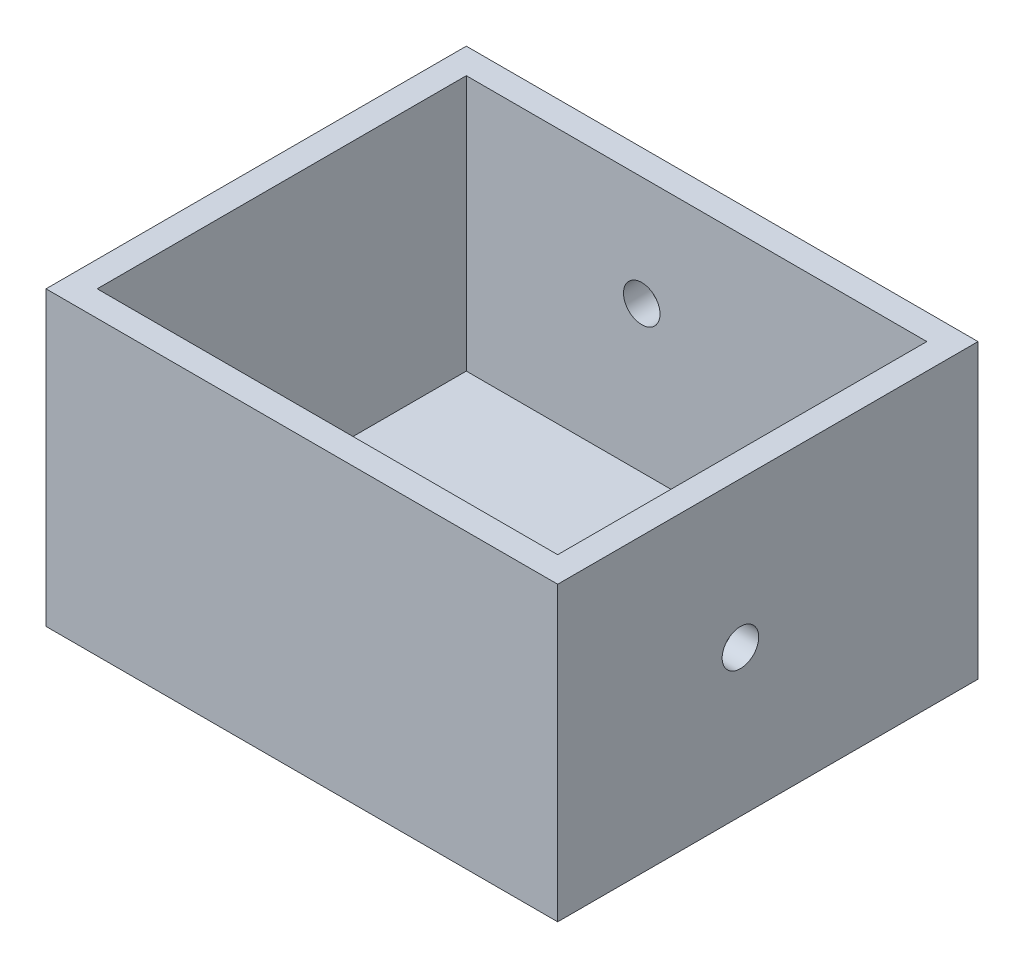
SolidWorks part; units mm, degrees
material "1060 Alloy"
ref_plane "Front Plane" through (0, 0, 0) normal (0, 0, 1) x (1, 0, 0)
ref_plane "Top Plane" through (0, 0, 0) normal (0, 1, 0) x (1, 0, 0)
ref_plane "Right Plane" through (0, 0, 0) normal (1, 0, 0) x (0, 0, -1)
sketch "Sketch1" plane through (0, 0, 0) normal (0, 1, 0) x (1, 0, 0)
  line L1 (-72.7163, -61.4091) -> (67.2837, -61.4091)
  line L2 (-72.7163, -61.4091) -> (-72.7163, 53.5909)
  line L3 (-72.7163, 53.5909) -> (67.2837, 53.5909)
  line L4 (67.2837, -61.4091) -> (67.2837, 53.5909)
  dimension "D1" = 140
  dimension "D2" = 115
extrude "Boss-Extrude1" add sketch "Sketch1" along normal blind 80
ref_plane "Plane1" through (0, 80, 0) normal (0, 1, 0) x (1, 0, 0)
sketch "Sketch2" plane through (0, 80, 0) normal (0, 1, 0) x (1, 0, 0)
  line L0 (67.2837, -61.4091) -> (67.2837, 53.5909) construction
  line L1 (-65.7163, -54.4091) -> (60.2837, -54.4091)
  line L2 (-65.7163, -54.4091) -> (-65.7163, 46.5909)
  line L3 (-65.7163, 46.5909) -> (60.2837, 46.5909)
  line L4 (60.2837, -54.4091) -> (60.2837, 46.5909)
  line L5 (67.2837, 53.5909) -> (-72.7163, 53.5909) construction
  line L6 (-72.7163, 53.5909) -> (-72.7163, -61.4091) construction
  line L7 (-72.7163, -61.4091) -> (67.2837, -61.4091) construction
  dimension "D1" = 7
  dimension "D2" = 7
  dimension "D3" = 7
  dimension "D4" = 7
extrude "Cut-Extrude1" cut sketch "Sketch2" against normal blind 70
ref_plane "Plane2" through (0, 0, -53.5909) normal (0, 0, -1) x (-1, 0, 0)
sketch "Sketch3" plane through (0, 0, -53.5909) normal (0, 0, -1) x (-1, 0, 0)
  line L1 (-67.2837, 80) -> (72.7163, 80) construction
  line L2 (-67.2837, 80) -> (-67.2837, 0) construction
  point P0 (17.7163, 50)
  point P1 (-42.2837, 50)
  dimension "D2" = 60
  dimension "D3" = 30
  dimension "D4" = 25
hole_wizard "M10x1.0 Tapped Hole1" positions "3DSketch1" profile "Sketch4" tap size "M10x1.0" standard "ANSI Metric"
sketch3d "3DSketch1"
  point P0 (-17.7163, 50, -53.5909)
  point P3 (42.2837, 50, -53.5909)
sketch "Sketch4" plane through (-17.7163, 50, -53.5909) normal (1, 0, 0) x (0, 1, 0)
  line L0 (0, 0) -> (0, 25.7039)
  line L1 (0, 25.7039) -> (4.5, 23)
  line L2 (4.5, 23) -> (4.5, 20)
  line L3 (4.5, 20) -> (5, 20)
  line L4 (5, 20) -> (5, 0)
  line L5 (5, 0) -> (0, 0)
  line L10 (0, 25.7039) -> (-4.5, 23) construction
  line L11 (0, -6.35) -> (0, 107.95) construction
  dimension "Tap Drill Dia." = 9
  dimension "Tap Drill Depth" = 23
  dimension "Thread Major Dia." = 10
  dimension "Thread Depth" = 20
  dimension "Drill Angle" = 118
ref_plane "Plane3" through (67.2837, 0, 0) normal (1, 0, 0) x (0, 0, -1)
sketch "Sketch5" plane through (67.2837, 0, 0) normal (1, 0, 0) x (0, 0, -1)
  line L0 (53.5909, 80) -> (53.5909, 0) construction
  line L1 (-61.4091, 80) -> (53.5909, 80) construction
  point P0 (-11.4091, 40)
  dimension "D1" = 65
  dimension "D2" = 40
hole_wizard "M10x1.0 Tapped Hole2" positions "3DSketch2" profile "Sketch6" tap size "M10x1.0" standard "ANSI Metric"
sketch3d "3DSketch2"
  point P0 (67.2837, 40, 11.4091)
sketch "Sketch6" plane through (67.2837, 40, 11.4091) normal (0, 1, 0) x (0, 0, -1)
  line L0 (0, 0) -> (0, 25.7039)
  line L1 (0, 25.7039) -> (4.5, 23)
  line L2 (4.5, 23) -> (4.5, 20)
  line L3 (4.5, 20) -> (5, 20)
  line L4 (5, 20) -> (5, 0)
  line L5 (5, 0) -> (0, 0)
  line L10 (0, 25.7039) -> (-4.5, 23) construction
  line L11 (0, -6.35) -> (0, 107.95) construction
  dimension "Tap Drill Dia." = 9
  dimension "Tap Drill Depth" = 23
  dimension "Thread Major Dia." = 10
  dimension "Thread Depth" = 20
  dimension "Drill Angle" = 118
